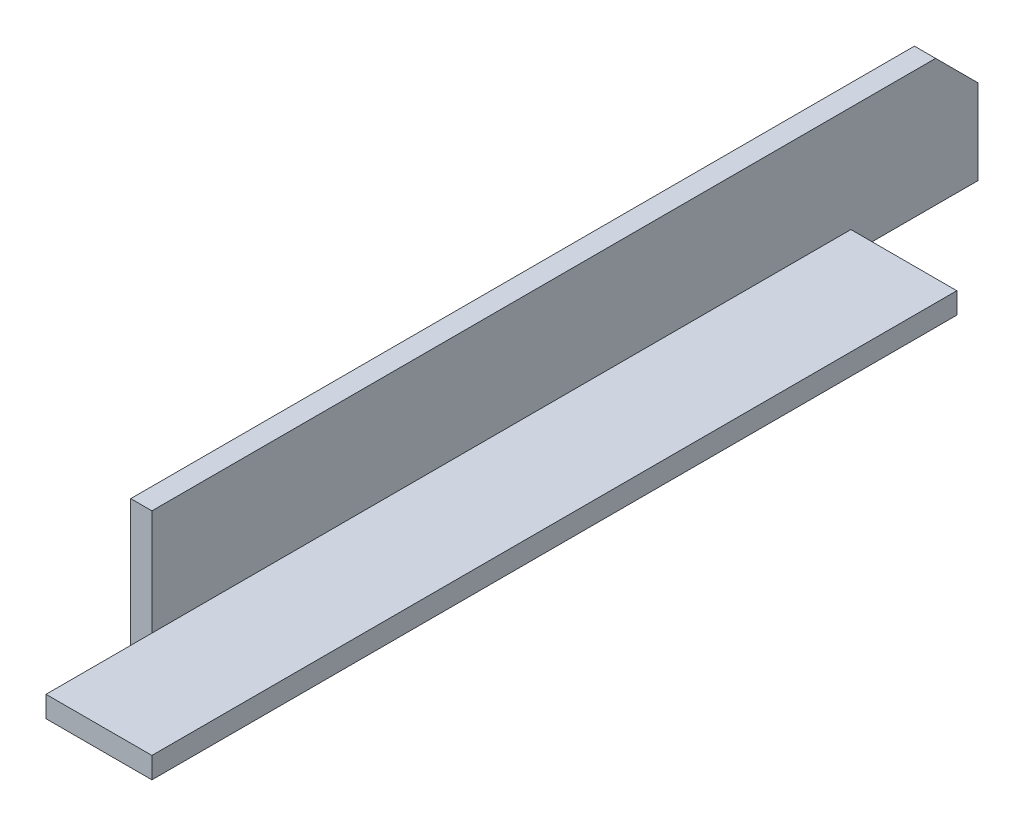
SolidWorks part; units mm, degrees
ref_plane "Front Plane" through (0, 0, 0) normal (0, 0, 1) x (1, 0, 0)
ref_plane "Top Plane" through (0, 0, 0) normal (0, 1, 0) x (1, 0, 0)
ref_plane "Right Plane" through (0, 0, 0) normal (1, 0, 0) x (0, 0, -1)
sketch "Sketch1" plane through (0, 0, 0) normal (0, 0, 1) x (1, 0, 0)
  line L0 (0, 0) -> (0, 38.1)
  line L1 (0, 38.1) -> (6.35, 38.1)
  line L2 (6.35, 38.1) -> (6.35, 6.35)
  line L3 (6.35, 6.35) -> (0, 0) construction
  line L4 (38.1, 6.35) -> (6.35, 6.35)
  line L5 (38.1, 0) -> (38.1, 6.35)
  line L6 (0, 0) -> (38.1, 0)
  dimension "D1" = 38.1
  dimension "D2" = 6.35
  dimension "D3" = 45
extrude "Boss-Extrude1" add sketch "Sketch1" along normal blind 279.4
sketch "Sketch2" plane through (0, 0, 0) normal (-1, 0, 0) x (0, 0, 1)
  line L0 (279.4, 0) -> (0, 0) construction
  line L1 (279.4, 38.1) -> (247.65, 38.1)
  line L2 (279.4, 38.1) -> (279.4, 0)
  line L3 (279.4, 0) -> (247.65, 0)
  line L4 (247.65, 38.1) -> (247.65, 0)
  dimension "D1" = 31.75
extrude "Cut-Extrude1" cut sketch "Sketch2" against normal blind 6.35
sketch "Sketch3" plane through (0, 0, 0) normal (0, -1, 0) x (1, 0, 0)
  line L0 (0, 247.65) -> (0, 0) construction
  line L1 (38.1, 0) -> (6.35, 0)
  line L2 (38.1, 0) -> (38.1, 38.1)
  line L3 (38.1, 38.1) -> (6.35, 38.1)
  line L4 (6.35, 0) -> (6.35, 38.1)
  dimension "D1" = 6.35
  dimension "D2" = 38.1
extrude "Cut-Extrude2" cut sketch "Sketch3" against normal through all
sketch "Sketch4" plane through (0, 0, 0) normal (-1, 0, 0) x (0, 0, 1)
  line L0 (0, 38.1) -> (0, 25.4)
  line L1 (0, 38.1) -> (0, 0) construction
  line L2 (0, 25.4) -> (12.7, 38.1)
  line L3 (247.65, 38.1) -> (0, 38.1) construction
  line L4 (12.7, 38.1) -> (0, 38.1)
  dimension "D1" = 12.7
extrude "Cut-Extrude3" cut sketch "Sketch4" against normal through all
